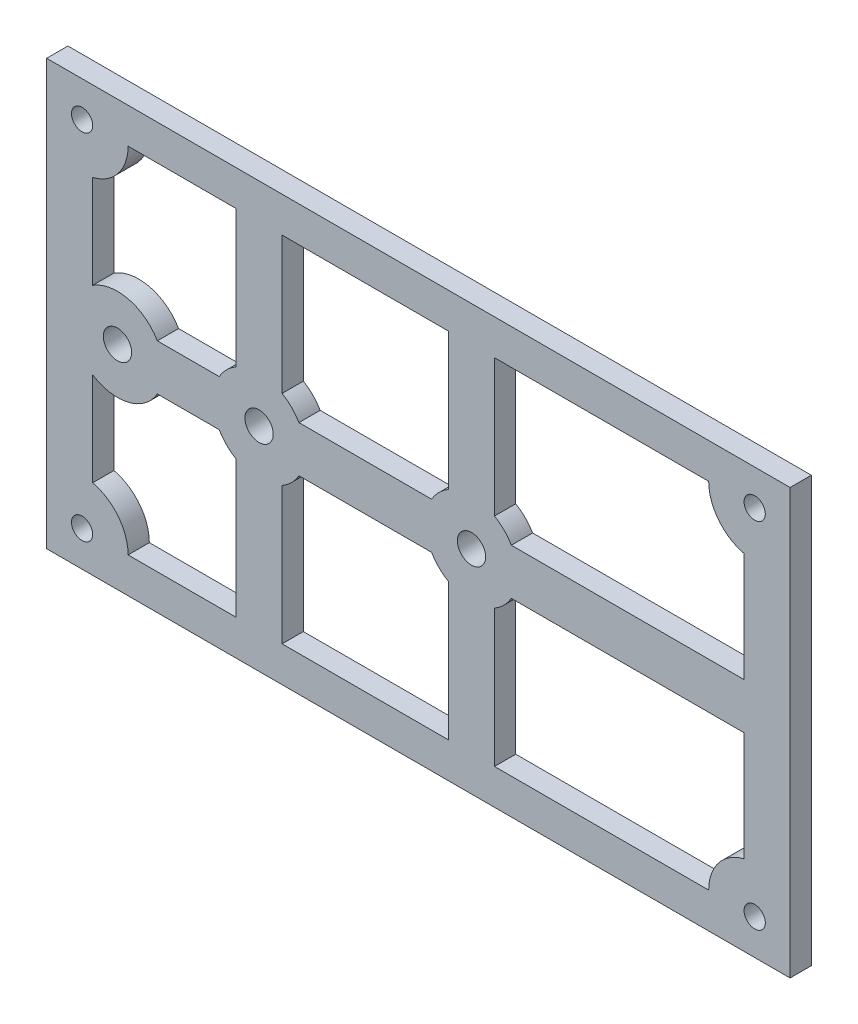
SolidWorks part; units mm, degrees
ref_plane "Front Plane" through (0, 0, 0) normal (0, 0, 1) x (1, 0, 0)
ref_plane "Top Plane" through (0, 0, 0) normal (0, 1, 0) x (1, 0, 0)
ref_plane "Right Plane" through (0, 0, 0) normal (1, 0, 0) x (0, 0, -1)
sketch "Sketch2" plane through (0, 0, 0) normal (0, 0, 1) x (1, 0, 0)
  line L0 (0, 30) -> (0, -30) construction
  line L1 (-52.5, -30) -> (52.5, -30)
  line L2 (-52.5, -30) -> (-52.5, 30)
  line L3 (-52.5, 30) -> (52.5, 30)
  line L4 (52.5, -30) -> (52.5, 30)
  line L5 (-52.5, -30) -> (52.5, 30) construction
  line L6 (-52.5, 30) -> (52.5, -30) construction
  line L7 (-52.5, 0) -> (52.5, 0) construction
  point P0 (0, 0)
  dimension "D1" = 105
  dimension "D2" = 60
extrude "Boss-Extrude1" add sketch "Sketch2" along normal blind 3
sketch "Sketch3" plane through (0, 0, 3) normal (0, 0, 1) x (1, 0, 0)
  line L0 (0, 30) -> (0, -30) construction
  line L1 (52.5, 30) -> (-52.5, 30) construction
  line L2 (-52.5, -30) -> (52.5, -30) construction
  line L3 (-52.5, 0) -> (52.5, 0) construction
  line L4 (-52.5, 30) -> (-52.5, -30) construction
  line L5 (52.5, -30) -> (52.5, 30) construction
  circle A0 centre (-47.5, 25) radius 1.5
  circle A1 centre (47.5, 25) radius 1.5
  circle A2 centre (47.5, -25) radius 1.5
  circle A3 centre (-47.5, -25) radius 1.5
  circle A4 centre (-42.5, 0) radius 2
  circle A5 centre (-22.5, 0) radius 2
  circle A6 centre (7.5, 0) radius 2
  dimension "D1" = 3
  dimension "D2" = 4
  dimension "D3" = 10
  dimension "D4" = 30
  dimension "D6" = 4
  dimension "D7" = 4
  dimension "D8" = 5
  dimension "D5" = 20
  dimension "D9" = 5
extrude "Cut-Extrude1" cut sketch "Sketch3" against normal through all
sketch "Sketch4" plane through (0, 0, 3) normal (0, 0, 1) x (1, 0, 0)
  line L0 (0, 30) -> (0, -30) construction
  line L1 (52.5, 30) -> (-52.5, 30) construction
  line L2 (-52.5, -30) -> (52.5, -30) construction
  line L3 (-52.5, 0) -> (52.5, 0) construction
  line L4 (-52.5, 30) -> (-52.5, -30) construction
  line L5 (52.5, -30) -> (52.5, 30) construction
  line L7 (-41, 25) -> (-25.75, 25)
  line L8 (-46, 18.6754) -> (-46, 5.4772)
  line L11 (-19.25, 25) -> (4.25, 25)
  line L20 (46, 18.6754) -> (46, 3.25)
  line L21 (41, 25) -> (10.75, 25)
  line L25 (-16.8708, 3.25) -> (1.8708, 3.25)
  line L27 (-25.75, 25) -> (-25.75, 5.6292)
  line L28 (-36.8708, 3.25) -> (-28.1292, 3.25)
  line L29 (-19.25, 25) -> (-19.25, 5.6292)
  line L31 (4.25, 25) -> (4.25, 5.6292)
  line L32 (-22.5, 0) -> (-22.5, 43.9564) construction
  line L34 (10.75, 25) -> (10.75, 5.6292)
  line L35 (46, 3.25) -> (13.1292, 3.25)
  line L36 (7.5, 0) -> (7.5, 48.1489) construction
  line L37 (46, -3.25) -> (13.1292, -3.25)
  line L38 (46, -18.6754) -> (46, -3.25)
  line L39 (41, -25) -> (10.75, -25)
  line L40 (10.75, -25) -> (10.75, -5.6292)
  line L41 (-16.8708, -3.25) -> (1.8708, -3.25)
  line L42 (4.25, -25) -> (4.25, -5.6292)
  line L43 (-19.25, -25) -> (-19.25, -5.6292)
  line L44 (-19.25, -25) -> (4.25, -25)
  line L45 (-46, -18.6754) -> (-46, -5.4772)
  line L46 (-36.8708, -3.25) -> (-28.1292, -3.25)
  line L47 (-25.75, -25) -> (-25.75, -5.6292)
  line L48 (-41, -25) -> (-25.75, -25)
  arc A0 (-46, 18.6754) -> (-41, 25) centre (-47.5, 25) ccw construction
  arc A1 (-41, 25) -> (-46, 18.6754) centre (-47.5, 25) cw
  arc A2 (-46, 5.4772) -> (-36.8708, 3.25) centre (-42.5, 0) cw
  circle A5 centre (-22.5, 0) radius 6.5 construction
  arc A6 (-28.1292, 3.25) -> (-25.75, 5.6292) centre (-22.5, 0) cw
  circle A7 centre (7.5, 0) radius 6.5 construction
  arc A8 (-36.8708, 3.25) -> (-46, 5.4772) centre (-42.5, 0) ccw construction
  arc A9 (41, 25) -> (46, 18.6754) centre (47.5, 25) ccw
  circle A10 centre (-22.5, 0) radius 6.5 construction
  arc A11 (1.8708, 3.25) -> (4.25, 5.6292) centre (7.5, 0) cw
  arc A13 (-19.25, 5.6292) -> (-16.8708, 3.25) centre (-22.5, 0) cw
  arc A15 (10.75, 5.6292) -> (13.1292, 3.25) centre (7.5, 0) cw
  arc A16 (41, -25) -> (46, -18.6754) centre (47.5, -25) cw
  arc A17 (10.75, -5.6292) -> (13.1292, -3.25) centre (7.5, 0) ccw
  arc A18 (1.8708, -3.25) -> (4.25, -5.6292) centre (7.5, 0) ccw
  arc A19 (-19.25, -5.6292) -> (-16.8708, -3.25) centre (-22.5, 0) ccw
  arc A20 (-46, -5.4772) -> (-36.8708, -3.25) centre (-42.5, 0) ccw
  arc A21 (-41, -25) -> (-46, -18.6754) centre (-47.5, -25) ccw
  arc A22 (-28.1292, -3.25) -> (-25.75, -5.6292) centre (-22.5, 0) ccw
  dimension "D4" = 13
  dimension "D3" = 13
  dimension "D5" = 13
  dimension "D6" = 13
  dimension "D1" = 6.5
  dimension "D2" = 6.5
  dimension "D7" = 6.5
  dimension "D8" = 6.5
  dimension "D9" = 6.5
extrude "Cut-Extrude2" cut sketch "Sketch4" against normal through all
